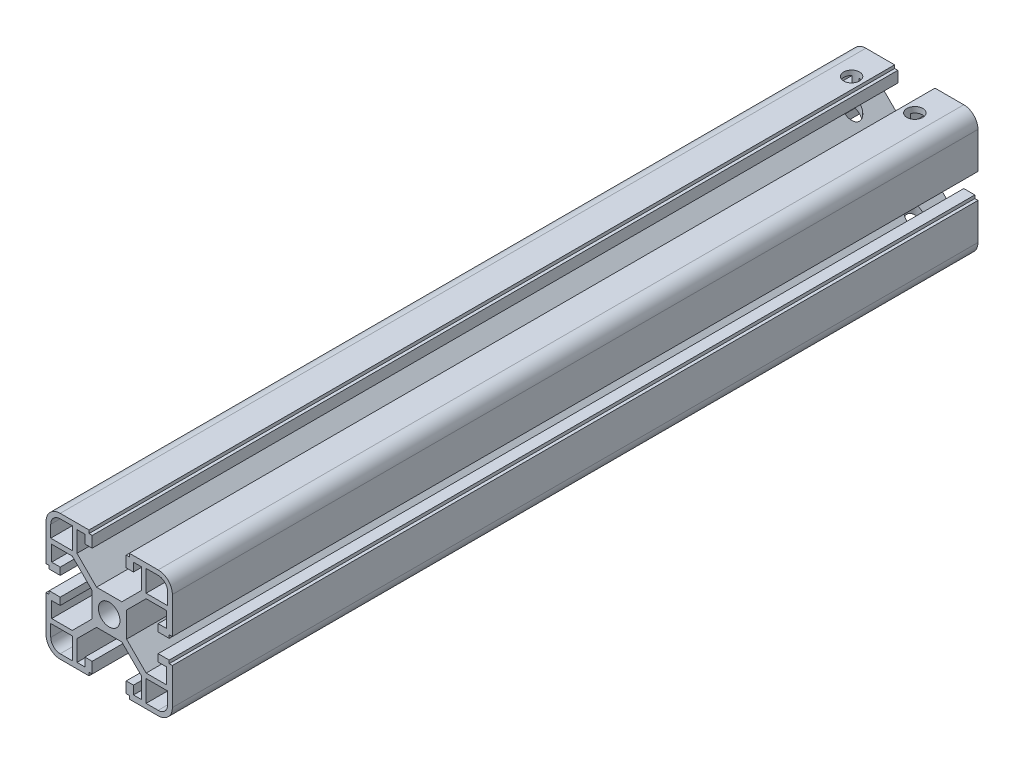
SolidWorks part; units mm, degrees
material "6061-T6 (SS)"
ref_plane "Front Plane" through (0, 0, 0) normal (0, 0, 1) x (1, 0, 0)
ref_plane "Top Plane" through (0, 0, 0) normal (0, 1, 0) x (1, 0, 0)
ref_plane "Right Plane" through (0, 0, 0) normal (1, 0, 0) x (0, 0, -1)
sketch "Sketch1" plane through (0, 0, 0) normal (0, 0, 1) x (1, 0, 0)
  line L0 (3.4, 0) -> (5.5, 0)
  line L1 (10.19, 11.69) -> (4, 5.5)
  line L2 (11.69, 10.19) -> (5.5, 4)
  line L3 (18.2, 10.19) -> (11.69, 10.19)
  line L4 (18.2, 10.19) -> (18.2, 5.2656)
  line L5 (18.2, 5.2656) -> (15.5, 5.2656)
  line L6 (15.5, 5.2656) -> (15.5, 2.9656)
  line L7 (15.5, 2.9656) -> (19, 2.9656)
  line L8 (19, 2.9656) -> (19, 3.9656)
  line L9 (19, 3.9656) -> (20, 3.9656)
  line L10 (20, 3.9656) -> (20, 15.5)
  line L11 (15.5, 20) -> (6.3853, 20)
  line L12 (18.5, 11.69) -> (18.5, 15.5)
  line L13 (15.5, 18.5) -> (11.69, 18.5)
  line L14 (11.69, 11.69) -> (11.69, 18.5)
  line L15 (0, 3.4) -> (0, 5.5)
  line L16 (4, 5.5) -> (0, 5.5)
  line L17 (6.3853, 20) -> (6.3853, 19)
  line L18 (5.5, 0) -> (5.5, 4)
  line L19 (6.3853, 19) -> (5.3853, 19)
  line L20 (5.3853, 19) -> (5.3853, 15.5)
  line L21 (5.3853, 15.5) -> (7.6853, 15.5)
  line L22 (10.19, 11.69) -> (10.19, 18.2)
  line L23 (11.69, 11.69) -> (18.5, 11.69)
  line L24 (7.6853, 18.2) -> (7.6853, 15.5)
  line L25 (10.19, 18.2) -> (7.6853, 18.2)
  arc A0 (20, 15.5) -> (15.5, 20) centre (15.5, 15.5) ccw
  arc A1 (18.5, 15.5) -> (15.5, 18.5) centre (15.5, 15.5) ccw
  arc A2 (3.4, 0) -> (0, 3.4) centre (0, 0) ccw
  dimension "D3" = 4.5
  dimension "D18" = 1.5
  dimension "D9" = 3.4
  dimension "D20" = 1.8
  dimension "D25" = 3
  dimension "D1" = 5.5
  dimension "D2" = 1.5
  dimension "D4" = 14.5
  dimension "D5" = 1.5
  dimension "D6" = 2.1
  dimension "D7" = 2.3
  dimension "D8" = 1.8
  dimension "D10" = 6.81
  dimension "D11" = 2.1
  dimension "D12" = 1
  dimension "D13" = 4.5
  dimension "D14" = 45
  dimension "D15" = 14.5
  dimension "D16" = 1
  dimension "D17" = 1.5
  dimension "D19" = 6.81
  dimension "D21" = 4.5
  dimension "D22" = 2.3
  dimension "D23" = 1
  dimension "D24" = 1
  dimension "D26" = 8.754
  dimension "D27" = 8.754
  dimension "D28" = 4.9244
  dimension "D29" = 2.5047
extrude "Boss-Extrude1" add sketch "Sketch1" along normal blind 255
mirror "Mirror1" about plane through (0, 0, 0) normal (0, 1, 0) of "Boss-Extrude1"
mirror "Mirror2" about plane through (0, 0, 0) normal (1, 0, 0) of "Boss-Extrude1"
mirror "Mirror3" about plane through (0, 0, 0) normal (0, 1, 0) of "Mirror2"
sketch "Sketch2" plane through (0, 5.5, 0) normal (0, 1, 0) x (1, 0, 0)
  line L0 (-15.5, -10) -> (15.5, -10) construction
  line L1 (-15.5, -255) -> (-15.5, 0) construction
  line L2 (15.5, -255) -> (15.5, 0) construction
  line L3 (-6.3853, 0) -> (-5.3853, 0) construction
  line L4 (0, 0) -> (0, -10) construction
  line L5 (4, 0) -> (-4, 0) construction
  circle A1 centre (-10, -10) radius 2.5
  circle A2 centre (10, -10) radius 2.5
  point P9 (-5.8853, 0)
  dimension "D1" = 10
  dimension "D2" = 10
  dimension "D3" = 5
extrude "Cut-Extrude1" cut sketch "Sketch2" against normal through all both and the other way through all
